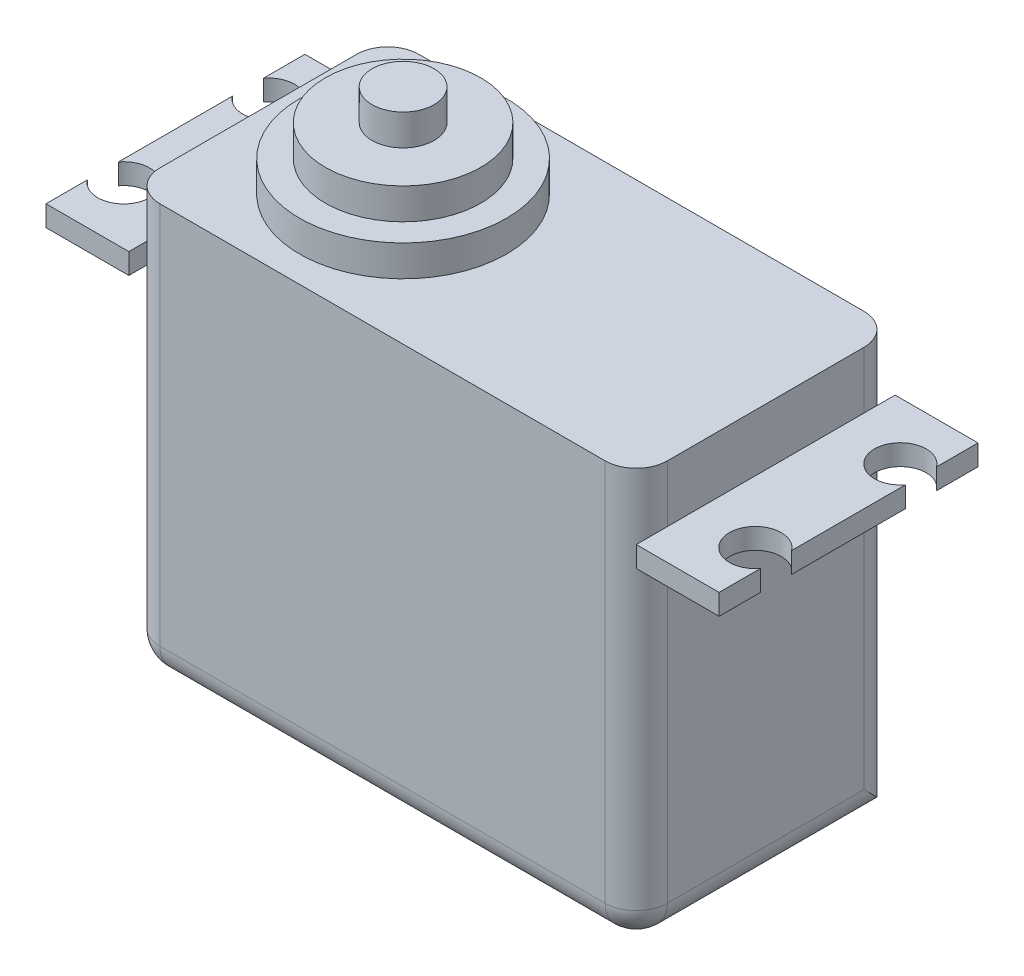
SolidWorks part; units mm, degrees
ref_plane "Front Plane" through (0, 0, 0) normal (0, 0, 1) x (1, 0, 0)
ref_plane "Top Plane" through (0, 0, 0) normal (0, 1, 0) x (1, 0, 0)
ref_plane "Right Plane" through (0, 0, 0) normal (1, 0, 0) x (0, 0, -1)
sketch "Sketch1" plane through (0, 0, 0) normal (0, 0, 1) x (1, 0, 0)
  line L1 (24.5, -20) -> (-24.5, -20)
  line L2 (24.5, -20) -> (24.5, 20)
  line L3 (24.5, 20) -> (-24.5, 20)
  line L4 (-24.5, -20) -> (-24.5, 20)
  line L5 (24.5, -20) -> (-24.5, 20) construction
  line L6 (24.5, 20) -> (-24.5, -20) construction
  point P0 (0, 0)
  dimension "D1" = 49
  dimension "D2" = 40
extrude "Boss-Extrude1" add sketch "Sketch1" along normal blind 25
sketch "Sketch4" plane through (0, 20, 0) normal (0, 1, 0) x (1, 0, 0)
  circle A0 centre (-10.5482, -12.4688) radius 10
  dimension "D1" = 20
extrude "Boss-Extrude2" add sketch "Sketch4" along normal blind 3
sketch "Sketch5" plane through (0, 23, 0) normal (0, 1, 0) x (1, 0, 0)
  circle A0 centre (-10.5482, -12.4688) radius 7.5
  circle A3 centre (-10.5482, -12.4688) radius 10 construction
  dimension "D1" = 15
extrude "Boss-Extrude3" add sketch "Sketch5" along normal blind 3
sketch "Sketch6" plane through (0, 26, 0) normal (0, 1, 0) x (1, 0, 0)
  circle A0 centre (-10.5482, -12.4688) radius 3
  circle A1 centre (-10.5482, -12.4688) radius 7.5 construction
  dimension "D1" = 6
extrude "Boss-Extrude4" add sketch "Sketch6" along normal blind 3
ref_plane "Plane1" through (0, 14.5, 0) normal (0, 1, 0) x (1, 0, 0)
sketch "Sketch7" plane through (0, 14.5, 0) normal (0, 1, 0) x (1, 0, 0)
  line L0 (-24.5, 0) -> (-32.5, 0)
  line L1 (-32.5, -4) -> (-32.5, 0)
  line L2 (-32.5, -18) -> (-32.5, -7)
  line L3 (-24.5, -25) -> (-32.5, -25)
  line L4 (-32.5, -25) -> (-32.5, -21)
  line L5 (-24.5, 0) -> (-24.5, -25)
  line L6 (-32.5, -12.5) -> (-19.5966, -12.5) construction
  line L7 (0, 0) -> (0, -36.6691) construction
  line L8 (24.5, 0) -> (24.5, -25)
  line L9 (24.5, -25) -> (32.5, -25)
  line L10 (32.5, -25) -> (32.5, -21)
  line L11 (32.5, -18) -> (32.5, -7)
  line L12 (32.5, -4) -> (32.5, 0)
  line L13 (24.5, 0) -> (32.5, 0)
  arc A0 (-32.5, -7) -> (-32.5, -4) centre (-30.5, -5.5) ccw
  arc A1 (-32.5, -18) -> (-32.5, -21) centre (-30.5, -19.5) cw
  arc A2 (32.5, -18) -> (32.5, -21) centre (30.5, -19.5) ccw
  arc A3 (32.5, -7) -> (32.5, -4) centre (30.5, -5.5) cw
  dimension "D2" = 5
  dimension "D1" = 8
  dimension "D3" = 6
  dimension "D4" = 5.5
fillet "Fillet1" radius 3 7 edges at (24.5, -20, 12.5) (24.5, 0, 0) (-24.5, -20, 12.5) (-24.5, 0, 0) (24.5, 0, 25) (0, -20, 25) (-24.5, 0, 25)
extrude "Boss-Extrude5" add sketch "Sketch7" against normal blind 2
